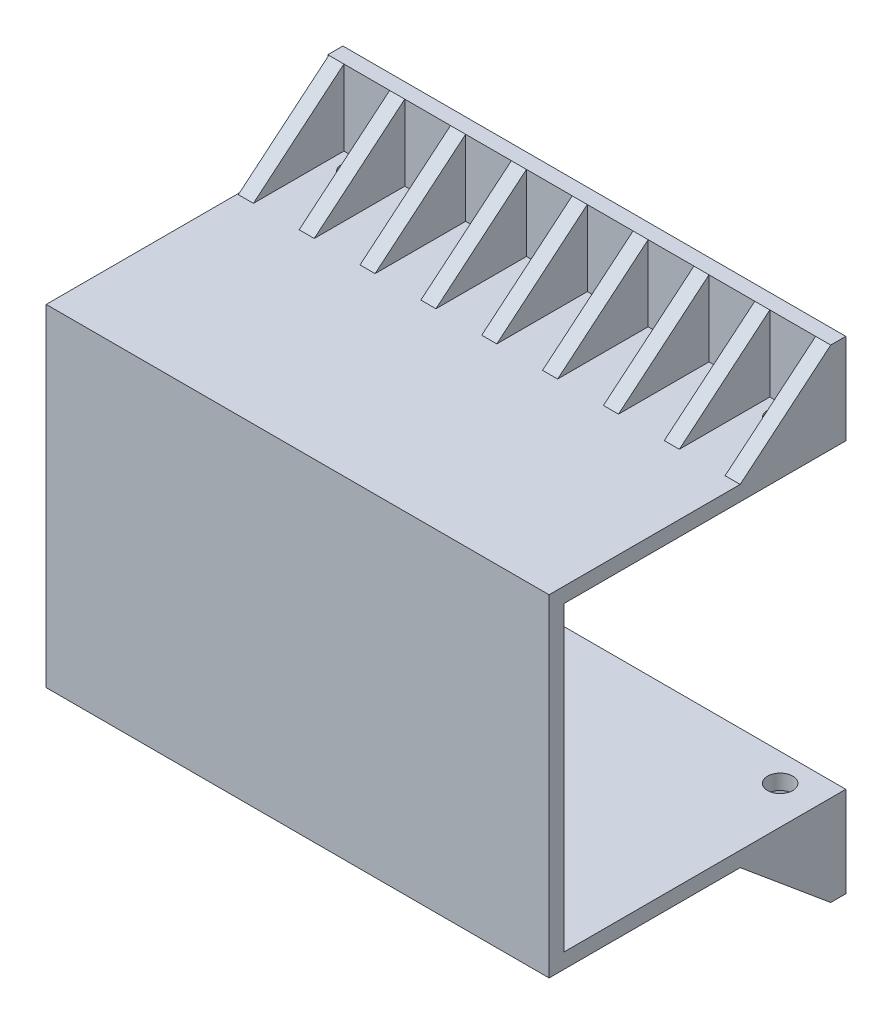
SolidWorks part; units mm, degrees
ref_plane "Front Plane" through (0, 0, 0) normal (0, 0, 1) x (1, 0, 0)
ref_plane "Top Plane" through (0, 0, 0) normal (0, 1, 0) x (1, 0, 0)
ref_plane "Right Plane" through (0, 0, 0) normal (1, 0, 0) x (0, 0, -1)
sketch "Sketch1" plane through (0, 0, 0) normal (0, 0, 1) x (1, 0, 0)
  line L0 (0, 0) -> (0, 60)
  line L1 (0, 60) -> (100, 60)
  line L2 (100, 60) -> (100, 0)
  line L3 (100, 0) -> (0, 0)
  dimension "D1" = 100
  dimension "D2" = 60
extrude "Boss-Extrude1" add sketch "Sketch1" along normal blind 3
sketch "Sketch2" plane through (0, 0, 0) normal (0, 0, -1) x (-1, 0, 0)
  line L0 (-100, 60) -> (0, 60) construction
  line L1 (-100, 60) -> (0, 60)
  line L2 (-100, 63) -> (0, 63)
  line L4 (0, 63) -> (0, 60)
  line L5 (0, -3) -> (-100, -3)
  line L6 (0, -3) -> (-100, -3)
  line L7 (-100, -3) -> (-100, 0)
  line L8 (0, -3) -> (0, 0)
  line L9 (-100, 63) -> (-100, 60)
  line M3 (-100, 0) -> (0, 0)
  line M5 (0, 60) -> (-100, 60)
  dimension "D1" = 3
  dimension "D2" = 3
extrude "Boss-Extrude2" add sketch "Sketch2" against normal blind 3 and the other way blind 53 contours L2 L9 L4 M5 | L6 L8 L7 M3
sketch "Sketch3" plane through (0, 0, -53) normal (0, 0, -1) x (-1, 0, 0)
  line L0 (0, 60) -> (-100, 60)
  line L1 (0, 60) -> (-100, 60) construction
  line L2 (-100, 60) -> (-100, 78)
  line L3 (-100, 78) -> (0, 78)
  line L4 (0, 78) -> (0, 60)
  line L5 (0, 30) -> (-100, 30) construction
  line L8 (0, 0) -> (-100, 0)
  line L9 (-100, 0) -> (-100, -18)
  line L10 (-100, -18) -> (0, -18)
  line L11 (0, -18) -> (0, 0)
  dimension "D1" = 18
extrude "Boss-Extrude3" add sketch "Sketch3" along normal blind 3
sketch "Sketch5" plane through (100, 0, 0) normal (1, 0, 0) x (0, 0, -1)
  line L0 (35, -3) -> (53, -3)
  line L1 (53, -3) -> (-3, -3) construction
  line L2 (53, -3) -> (53, -18)
  line L3 (53, -18) -> (35, -3)
  dimension "D1" = 18
extrude "Boss-Extrude4" add sketch "Sketch5" against normal blind 3
sketch "Sketch6" plane through (0, -3, 0) normal (0, -1, 0) x (1, 0, 0)
  line L0 (97, -35) -> (97, -53)
  line L1 (97, -53) -> (0, -53)
  line L2 (0, -53) -> (0, 3) construction
  line L3 (0, -53) -> (97, -53) construction
  line L4 (0, -53) -> (0, -35)
  line L5 (0, -35) -> (97, -35)
extrude "Boss-Extrude5" add sketch "Sketch6" against normal blind 3
pattern_linear "LPattern4" count 9 spacing 12.1 along (-1, 0, 0) of "Boss-Extrude4"
sketch "Sketch7" plane through (0, -3, 0) normal (0, -1, 0) x (1, 0, 0)
  line L0 (87.9, -53) -> (97, -53) construction
  line L1 (97, -53) -> (97, -35) construction
  line L3 (12.3, -53) -> (12.3, -35) construction
  line L4 (3.2, -53) -> (12.3, -53) construction
  circle A0 centre (92.45, -50.5) radius 2.5
  circle A1 centre (7.75, -50.5) radius 2.5
  dimension "D1" = 5
  dimension "D2" = 4.55
  dimension "D4" = 4.55
extrude "Cut-Extrude2" cut sketch "Sketch7" against normal through all
ref_plane "Plane1" through (0, 63, 3) normal (0, -1, 0) x (-1, 0, 0)
sketch "Sketch10" plane through (0, 0, 0) normal (-1, 0, 0) x (0, 0, 1)
  line L0 (0, 30) -> (3, 30)
  line L1 (0, 60) -> (0, 0) construction
  line L2 (3, 63) -> (3, -3) construction
  line L3 (3, 30) -> (3, 114.1377)
  line L4 (3, 114.1377) -> (-76.8566, 109.7379)
  line L5 (-76.8566, 109.7379) -> (-70.7999, 33.223)
  line L6 (-70.7999, 33.223) -> (0, 30)
extrude "Cut-Extrude4" cut sketch "Sketch10" against normal through all
mirror "Mirror2" about plane through (100, 30, 0) normal (0, -1, 0) of bodies 111
